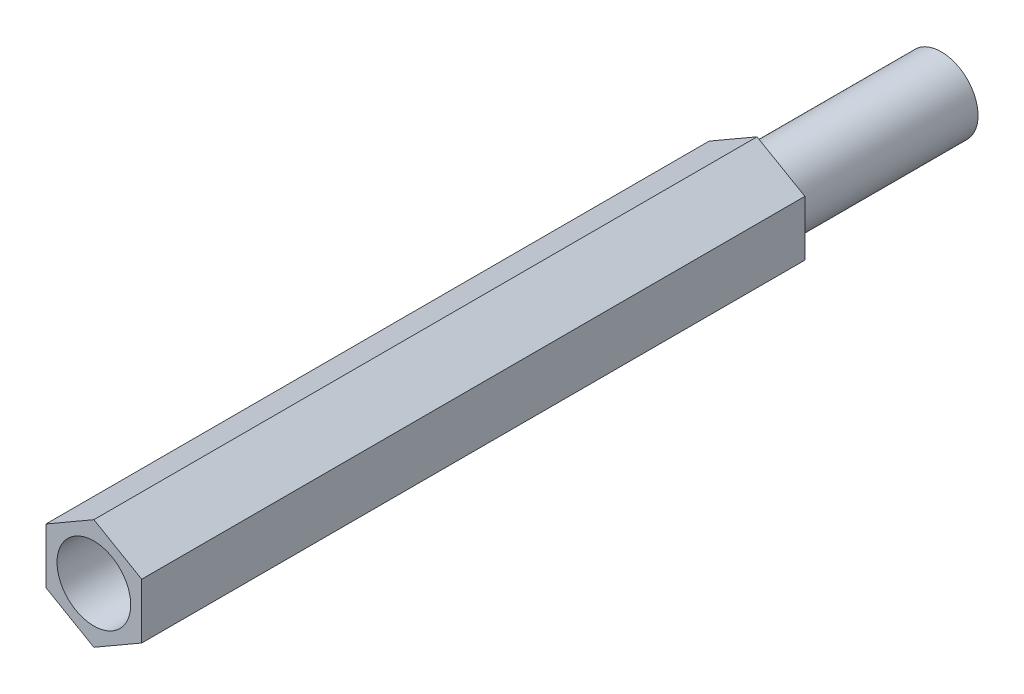
SolidWorks part; units mm, degrees
material "Alloy Steel (SS)"
ref_plane "Front Plane" through (0, 0, 0) normal (0, 0, 1) x (1, 0, 0)
ref_plane "Top Plane" through (0, 0, 0) normal (0, 1, 0) x (1, 0, 0)
ref_plane "Right Plane" through (0, 0, 0) normal (1, 0, 0) x (0, 0, -1)
sketch "Sketch1" plane through (0, 0, 0) normal (0, 0, 1) x (1, 0, 0)
  line L1 (0, 3) -> (-2.5981, 1.5)
  line L2 (-2.5981, 1.5) -> (-2.5981, -1.5)
  line L3 (-2.5981, -1.5) -> (0, -3)
  line L4 (0, -3) -> (2.5981, -1.5)
  line L5 (2.5981, -1.5) -> (2.5981, 1.5)
  line L6 (2.5981, 1.5) -> (0, 3)
  circle A0 centre (0, 0) radius 2.5981 construction
  circle A1 centre (0, 0) radius 3
  dimension "D1" = 6
extrude "Boss-Extrude1" add sketch "Sketch1" against normal blind 36 contours L5 L6 L1 L2 L3 L4
sketch "Sketch2" plane through (0, 0, 0) normal (0, 0, 1) x (1, 0, 0)
  circle A0 centre (0, 0) radius 2
  dimension "D1" = 4
extrude "Cut-Extrude1" cut sketch "Sketch2" against normal blind 29
sketch "Sketch3" plane through (0, 0, -36) normal (0, 0, -1) x (-1, 0, 0)
  circle A0 centre (0, 0) radius 2
  dimension "D1" = 4
extrude "Boss-Extrude2" add sketch "Sketch3" along normal blind 10
